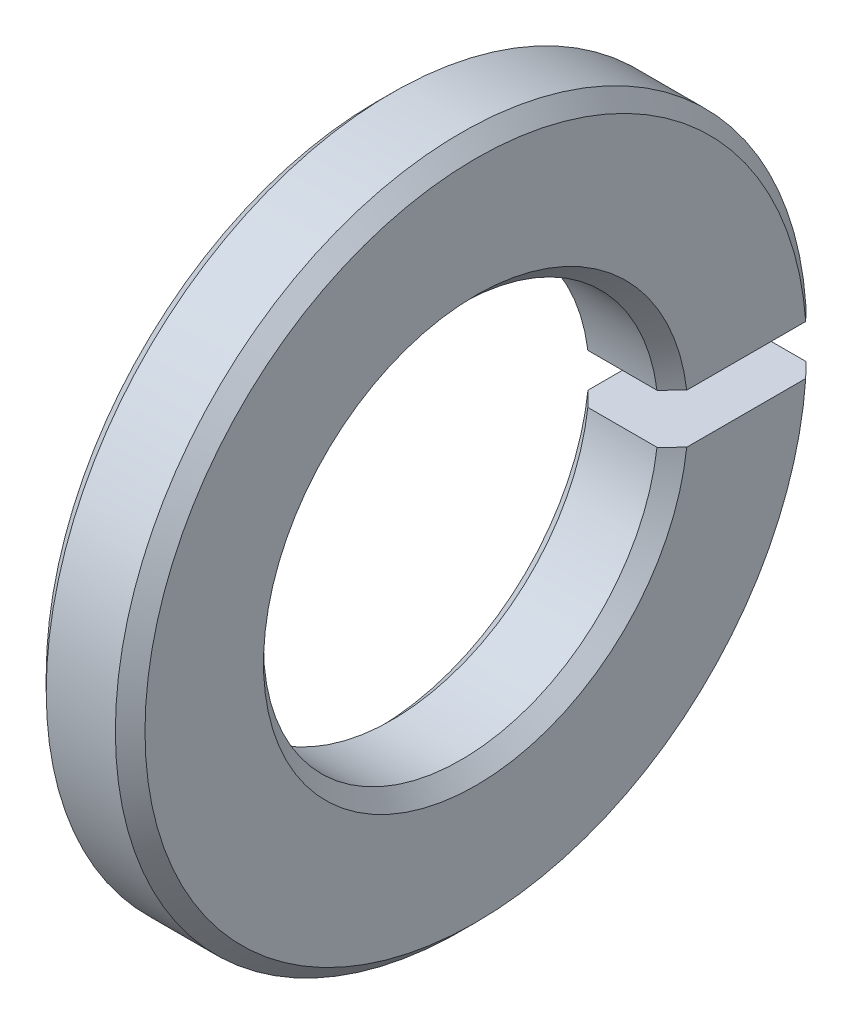
SolidWorks part; units mm, degrees
material "AISI 304"
ref_plane "Front" through (0, 0, 0) normal (0, 0, 1) x (1, 0, 0)
ref_plane "Top" through (0, 0, 0) normal (0, 1, 0) x (1, 0, 0)
ref_plane "Right" through (0, 0, 0) normal (1, 0, 0) x (0, 0, -1)
sketch "Sketch1" plane through (0, 0, 0) normal (1, 0, 0) x (0, 0, -1)
  line L1 (3.9686, 0.5) -> (6.9821, 0.5)
  line L2 (3.9686, -0.5) -> (6.9821, -0.5)
  arc A0 (3.9686, 0.5) -> (3.9686, -0.5) centre (0, 0) ccw
  arc A1 (6.9821, 0.5) -> (6.9821, -0.5) centre (0, 0) ccw
  dimension "D1" = 8
  dimension "D2" = 3
  dimension "D4" = 1
extrude "Boss-Extrude1" add sketch "Sketch1" along normal blind 2
chamfer "Chamfer1" distance 0.3 angle 45 4 edges at (0, 0, 4) (2, 0, 4) (0, 0, 7) (2, 0, 7)
